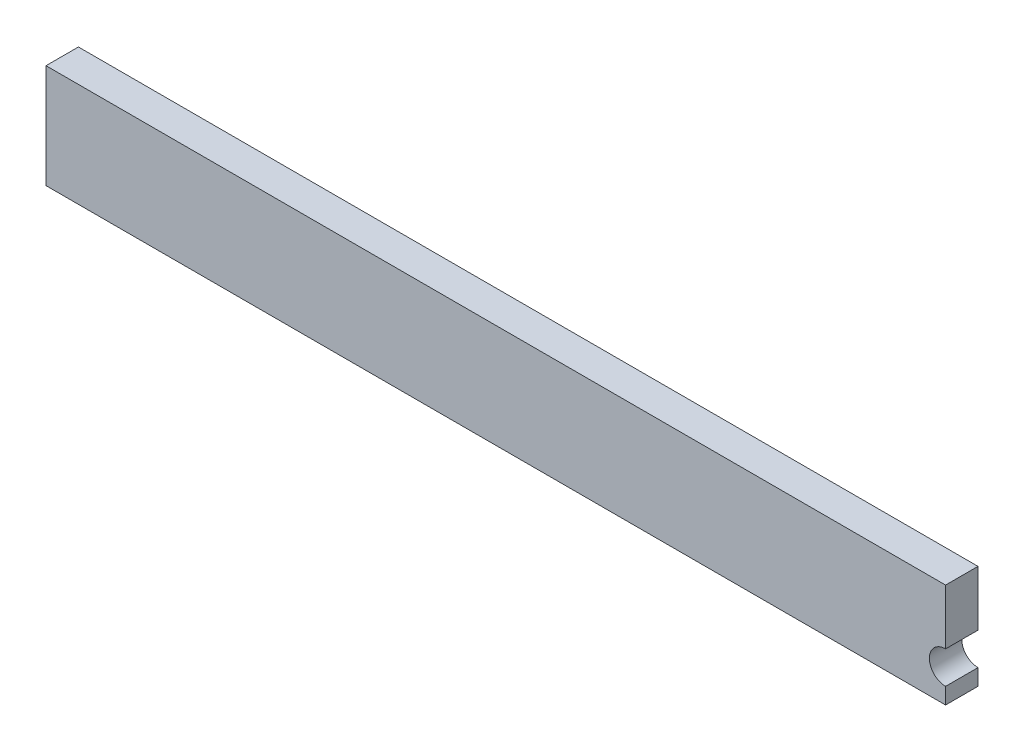
SolidWorks part; units mm, degrees
ref_plane "Спереди" through (0, 0, 0) normal (0, 0, 1) x (1, 0, 0)
ref_plane "Сверху" through (0, 0, 0) normal (0, 1, 0) x (1, 0, 0)
ref_plane "Справа" through (0, 0, 0) normal (1, 0, 0) x (0, 0, -1)
other "Configuration Table"
sketch "Эскиз1" plane through (0, 0, 0) normal (0, 0, 1) x (1, 0, 0)
  line L1 (0, 0) -> (55.5, 0)
  line L2 (0, 0) -> (0, 6.41)
  line L3 (0, 6.41) -> (55.5, 6.41)
  line L4 (55.5, 0) -> (55.5, 6.41)
  circle A1 centre (55.5, 2) radius 1
  point P7 (0, 0)
  dimension "D3" = 2
  dimension "D1" = 6.41
  dimension "D2" = 55.5
  dimension "D4" = 2
extrude "Бобышка-Вытянуть1" add sketch "Эскиз1" along normal blind 2 contours A1 L4 L3 L2 L1
